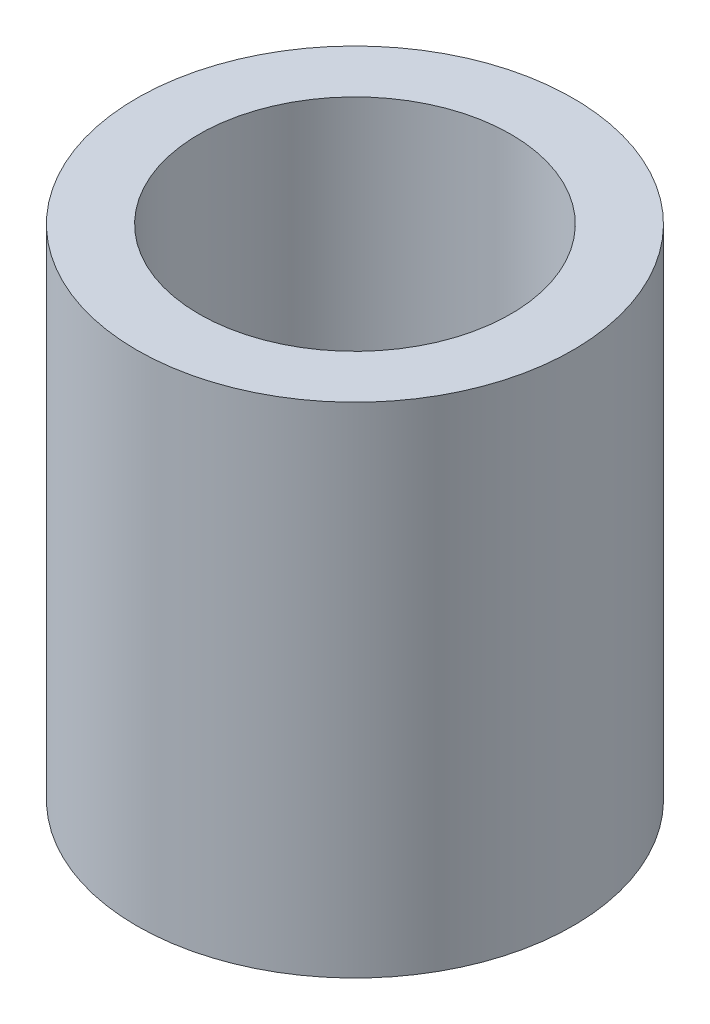
SolidWorks part; units mm, degrees
ref_plane "Front Plane" through (0, 0, 0) normal (0, 0, 1) x (1, 0, 0)
ref_plane "Top Plane" through (0, 0, 0) normal (0, 1, 0) x (1, 0, 0)
ref_plane "Right Plane" through (0, 0, 0) normal (1, 0, 0) x (0, 0, -1)
sketch "Sketch1" plane through (0, 0, 0) normal (0, 1, 0) x (1, 0, 0)
  circle A0 centre (0, 0) radius 7.9375
  circle A1 centre (0, 0) radius 11.1125
  dimension "D1" = 22.225
  dimension "D2" = 15.875
extrude "Boss-Extrude1" add sketch "Sketch1" along normal blind 25.4
